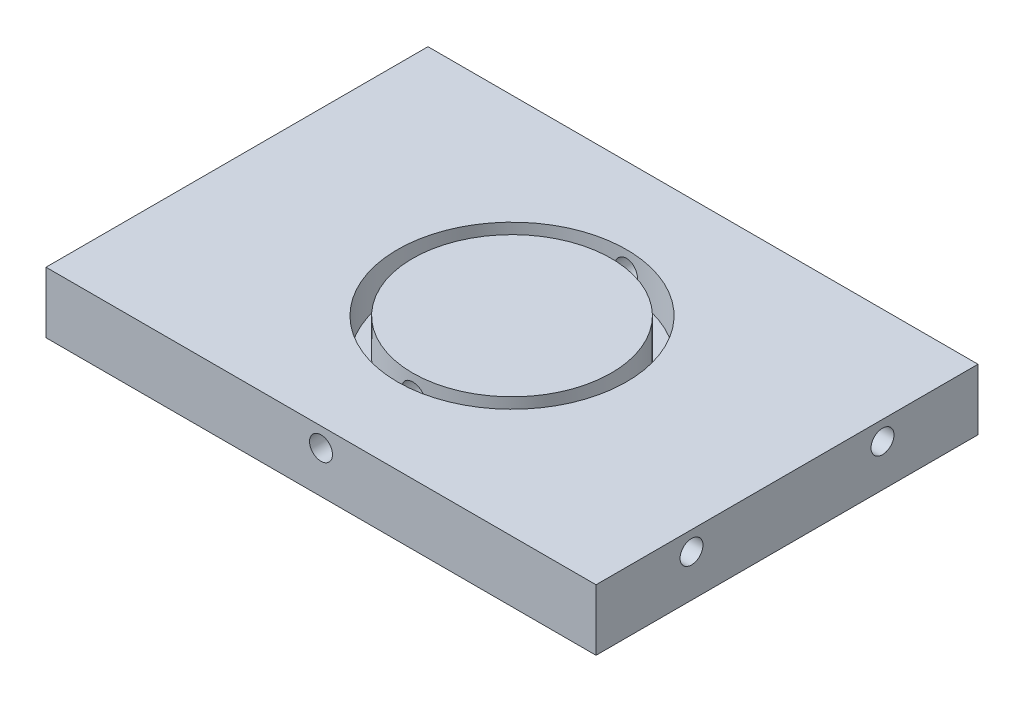
SolidWorks part; units mm, degrees
ref_plane "Plan de face" through (0, 0, 0) normal (0, 0, 1) x (1, 0, 0)
ref_plane "Plan de dessus" through (0, 0, 0) normal (0, 1, 0) x (1, 0, 0)
ref_plane "Plan de droite" through (0, 0, 0) normal (1, 0, 0) x (0, 0, -1)
sketch "Esquisse1" plane through (0, 0, 0) normal (0, 0, 1) x (1, 0, 0)
  line L0 (-5.5, -49) -> (66.5, -49) construction
  line L5 (-5.5, -45) -> (66.5, -45)
  line L6 (-5.5, -45) -> (-5.5, -53)
  line L7 (-5.5, -53) -> (66.5, -53)
  line L8 (66.5, -45) -> (66.5, -53)
  line L9 (30.5, -45) -> (30.5, -53) construction
  dimension "D1" = 8
  dimension "D2" = 72
extrude "Boss.-Extru.1" add sketch "Esquisse1" along normal blind 50
sketch "Esquisse2" plane through (0, -45, 0) normal (0, 1, 0) x (-1, 0, 0)
  line L0 (5.5, 50) -> (-66.5, 50) construction
  line L7 (-66.5, 50) -> (-66.5, 0) construction
  circle A0 centre (-30.5, 25) radius 15
  circle A2 centre (-30.5, 25) radius 13
  dimension "D10" = 36
  dimension "D11" = 25
extrude "Enlèv. mat.-Extru.1" cut sketch "Esquisse2" against normal blind 5
sketch "Esquisse3" plane through (-5.5, 0, 0) normal (-1, 0, 0) x (0, 0, 1)
  line L0 (50, -53) -> (0, -53) construction
  line L1 (0, -45) -> (0, -53) construction
  line L2 (50, -45) -> (50, -53) construction
  circle A0 centre (12.5, -47.5) radius 1.5
  circle A1 centre (37.5, -47.5) radius 1.5
  dimension "D1" = 5.5
  dimension "D2" = 5.5
  dimension "D3" = 12.5
  dimension "D4" = 12.5
extrude "Enlèv. mat.-Extru.2" cut sketch "Esquisse3" against normal blind 10
sketch "Esquisse4" plane through (66.5, 0, 0) normal (1, 0, 0) x (0, 0, -1)
  line L0 (-50, -53) -> (0, -53) construction
  line L1 (-50, -45) -> (-50, -53) construction
  line L2 (0, -45) -> (0, -53) construction
  circle A0 centre (-37.5, -47.5) radius 1.5
  circle A1 centre (-12.5, -47.5) radius 1.5
  dimension "D1" = 5.5
  dimension "D2" = 5.5
  dimension "D3" = 12.5
  dimension "D4" = 12.5
extrude "Enlèv. mat.-Extru.3" cut sketch "Esquisse4" against normal blind 10
sketch "Esquisse5" plane through (0, 0, 0) normal (0, 0, -1) x (-1, 0, 0)
  line L0 (5.5, -45) -> (-66.5, -45) construction
  line L1 (-66.5, -45) -> (-66.5, -53) construction
  circle A0 centre (-30.5, -47.5) radius 1.5
  dimension "D1" = 2.5
  dimension "D2" = 36
extrude "Enlèv. mat.-Extru.4" cut sketch "Esquisse5" against normal through all
